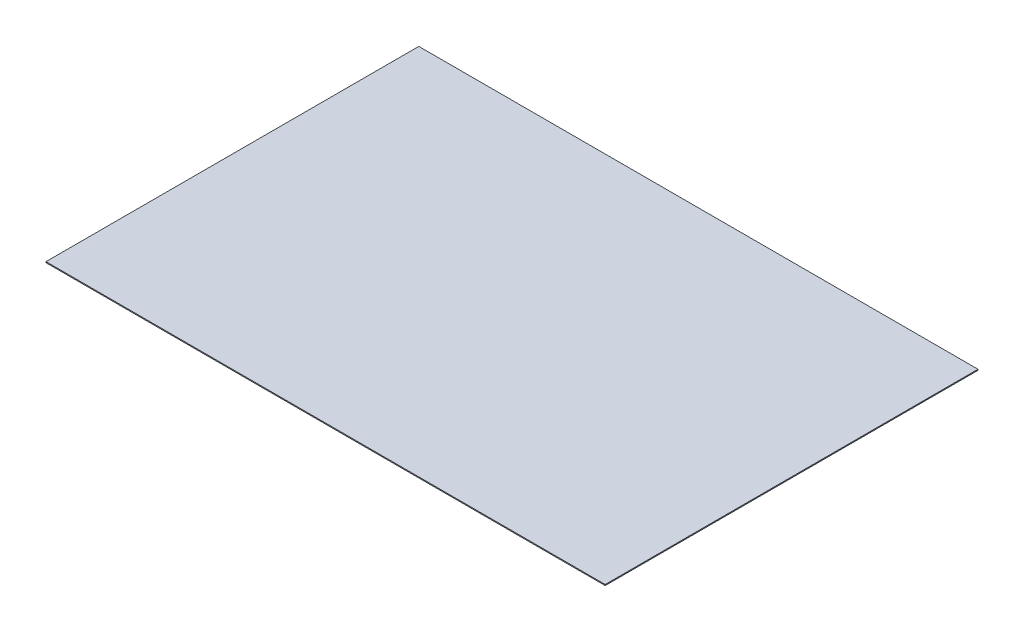
SolidWorks part; units mm, degrees
ref_plane "Front Plane" through (0, 0, 0) normal (0, 0, 1) x (1, 0, 0)
ref_plane "Top Plane" through (0, 0, 0) normal (0, 1, 0) x (1, 0, 0)
ref_plane "Right Plane" through (0, 0, 0) normal (1, 0, 0) x (0, 0, -1)
sketch "Sketch1" plane through (0, 0, 0) normal (0, 1, 0) x (1, 0, 0)
  line L1 (0, 0) -> (3657.6, 0)
  line L2 (0, 0) -> (0, 2438.4)
  line L3 (0, 2438.4) -> (3657.6, 2438.4)
  line L4 (3657.6, 0) -> (3657.6, 2438.4)
  dimension "D1" = 2438.4
  dimension "D2" = 3657.6
extrude "Boss-Extrude1" add sketch "Sketch1" along normal blind 6.35
sketch "Sketch3" plane through (0, 6.35, 0) normal (0, 1, 0) x (1, 0, 0)
  line L0 (0, 2438.4) -> (0, 0) construction
  line L1 (6.35, 2432.05) -> (3651.25, 2432.05)
  line L2 (6.35, 2432.05) -> (6.35, 6.35)
  line L3 (6.35, 6.35) -> (3651.25, 6.35)
  line L4 (3651.25, 2432.05) -> (3651.25, 6.35)
  line L5 (0, 0) -> (3657.6, 0) construction
  line L6 (3657.6, 0) -> (3657.6, 2438.4) construction
  line L7 (3657.6, 2438.4) -> (0, 2438.4) construction
  line L9 (0, 2438.4) -> (3657.6, 2438.4)
  line L10 (0, 2438.4) -> (0, 0)
  line L11 (0, 0) -> (3657.6, 0)
  line L12 (3657.6, 2438.4) -> (3657.6, 0)
  point P17 (3657.6, 0)
  dimension "D1" = 6.35
  dimension "D2" = 6.35
  dimension "D3" = 6.35
  dimension "D4" = 6.35
extrude "Boss-Extrude2" [suppressed] add sketch "Sketch3" along normal blind 76.2
sketch "Sketch4" [suppressed] plane through (0, 6.35, 0) normal (0, 1, 0) x (1, 0, 0)
  line L1 (6.35, 2432.05) -> (3651.25, 2432.05)
  line L2 (6.35, 2432.05) -> (6.35, 6.35)
  line L3 (6.35, 6.35) -> (3651.25, 6.35)
  line L4 (3651.25, 2432.05) -> (3651.25, 6.35)
  point P5 (3651.25, 6.35)
extrude "Cut-Extrude1" [suppressed] cut sketch "Sketch4" against normal through all
